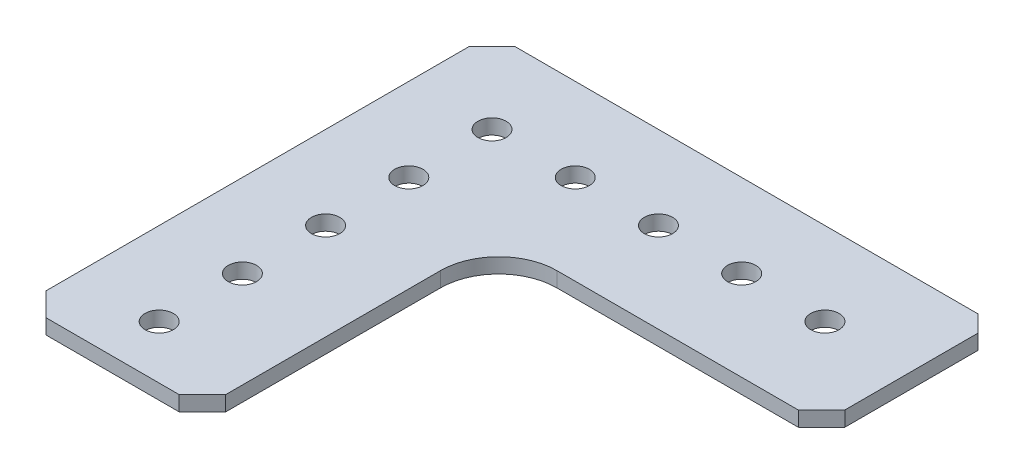
SolidWorks part; units mm, degrees
ref_plane "Front Plane" through (0, 0, 0) normal (0, 0, 1) x (1, 0, 0)
ref_plane "Top Plane" through (0, 0, 0) normal (0, 1, 0) x (1, 0, 0)
ref_plane "Right Plane" through (0, 0, 0) normal (1, 0, 0) x (0, 0, -1)
sketch "Sketch1" plane through (0, 0, 0) normal (0, 1, 0) x (1, 0, 0)
  line L0 (-93.8325, 46.7526) -> (-93.8325, -17.7634)
  line L5 (-90.2765, 50.3086) -> (-19.6645, 50.3086)
  line L6 (-90.2765, -21.3194) -> (-69.9565, -21.3194)
  line L7 (-66.4005, -17.7634) -> (-66.4005, 15.0026)
  line L8 (-17.1245, 47.7686) -> (-17.1245, 27.4486)
  line L9 (-90.2765, 50.3086) -> (-93.8325, 46.7526)
  line L10 (-93.8325, -17.7634) -> (-90.2765, -21.3194)
  line L11 (-69.9565, -21.3194) -> (-66.4005, -17.7634)
  line L12 (-19.6645, 50.3086) -> (-17.1245, 47.7686)
  line L13 (-20.6805, 23.8926) -> (-57.5105, 23.8926)
  line L14 (-17.1245, 27.4486) -> (-20.6805, 23.8926)
  arc A0 (-57.5105, 23.8926) -> (-66.4005, 15.0026) centre (-57.5105, 15.0026) ccw
  point P0 (-93.8325, 50.3086)
  point P1 (-93.8325, -21.3194)
  point P2 (-17.1245, 50.3086)
  point P3 (-66.4005, -21.3194)
  point P6 (-17.1245, 23.8926)
  dimension "D1" = 8.89
  dimension "D2" = 70.612
extrude "Boss-Extrude1" add sketch "Sketch1" along normal blind 2.286
sketch "Sketch2" plane through (0, 2.286, 0) normal (0, 1, 0) x (1, 0, 0)
  line L0 (-93.8325, 46.7526) -> (-93.8325, -17.7634) construction
  line L1 (-19.6645, 50.3086) -> (-90.2765, 50.3086) construction
  circle A0 centre (-81.1325, 37.6086) radius 2.159
  circle A1 centre (-81.1325, 24.9086) radius 2.159
  circle A2 centre (-81.1325, 12.2086) radius 2.159
  circle A3 centre (-81.1325, -0.4914) radius 2.159
  circle A4 centre (-81.1325, -13.1914) radius 2.159
  circle A5 centre (-68.4325, 37.6086) radius 2.159
  circle A6 centre (-55.7325, 37.6086) radius 2.159
  circle A7 centre (-43.0325, 37.6086) radius 2.159
  circle A8 centre (-30.3325, 37.6086) radius 2.159
  dimension "D1" = 12.7
  dimension "D2" = 12.7
  dimension "D3" = 5
extrude "Cut-Extrude1" cut sketch "Sketch2" against normal blind 2.286
